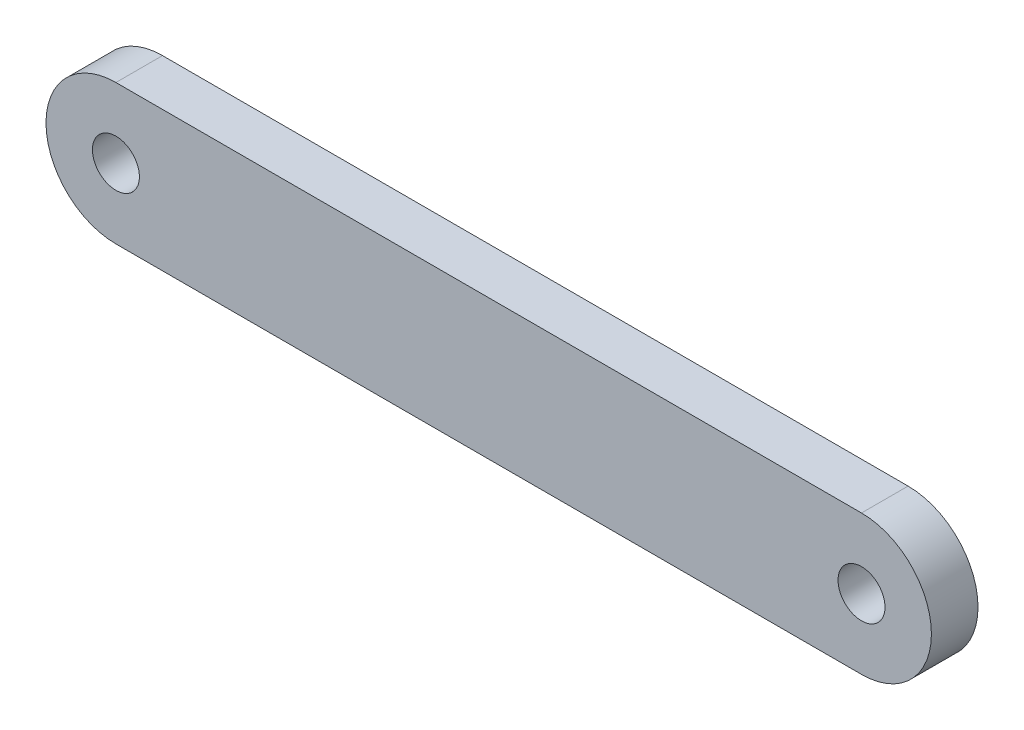
SolidWorks part; units mm, degrees
material "Free-Cutting Brass, UNS C36000"
ref_plane "Front Plane" through (0, 0, 0) normal (0, 0, 1) x (1, 0, 0)
ref_plane "Top Plane" through (0, 0, 0) normal (0, 1, 0) x (1, 0, 0)
ref_plane "Right Plane" through (0, 0, 0) normal (1, 0, 0) x (0, 0, -1)
other "Configuration Table"
sketch "Sketch1" plane through (0, 0, 0) normal (0, 0, 1) x (1, 0, 0)
  line L0 (-25.4, 0) -> (25.4, 0) construction
  line L4 (-25.4, 4.7625) -> (25.4, 4.7625)
  line L5 (-25.4, -4.7625) -> (25.4, -4.7625)
  arc A2 (-25.4, 4.7625) -> (-25.4, -4.7625) centre (-25.4, 0) ccw
  arc A3 (25.4, -4.7625) -> (25.4, 4.7625) centre (25.4, 0) ccw
  point P5 (0, 0)
  dimension "D1" = 9.525
  dimension "D2" = 50.8
extrude "Boss-Extrude1" add sketch "Sketch1" along normal mid plane 3.175
sketch "Sketch2" plane through (0, 0, 1.5875) normal (0, 0, 1) x (1, 0, 0)
  point P0 (-25.4, 0)
  point P3 (25.4, 0)
hole_wizard "1/8 (0.126) Dowel Hole1" positions "Sketch2" profile "Sketch3" hole size "1/8" standard "ANSI Inch" end condition through all
sketch "Sketch3" plane through (-25.4, 0, 1.5875) normal (1, 0, 0) x (0, -1, 0)
  line L0 (0, 0) -> (0, 3.175)
  line L1 (0, 3.175) -> (1.6002, 3.175)
  line L2 (1.6002, 3.175) -> (1.6002, 0)
  line L5 (1.6002, 0) -> (0, 0)
  line L11 (0, -6.35) -> (0, 107.95) construction
  dimension "Thru Hole Dia." = 3.2004
  dimension "Thru Hole Depth" = 3.175
